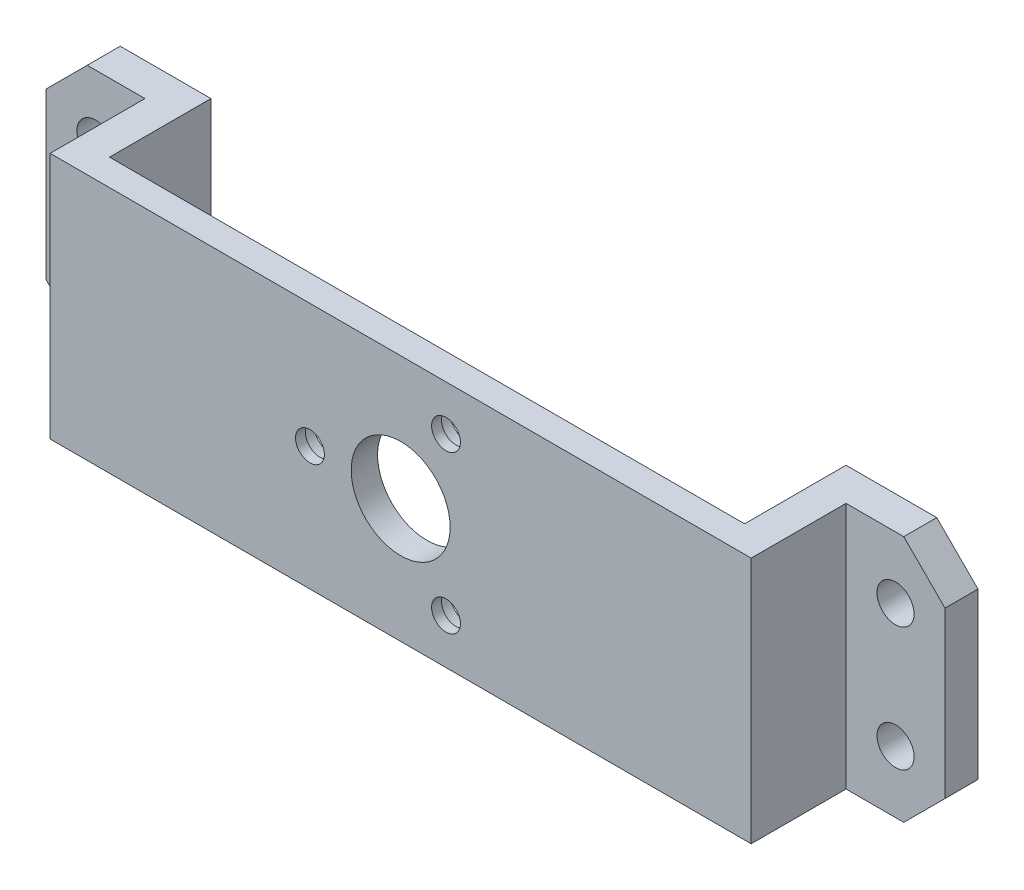
SolidWorks part; units mm, degrees
ref_plane "Front Plane" through (0, 0, 0) normal (0, 0, 1) x (1, 0, 0)
ref_plane "Top Plane" through (0, 0, 0) normal (0, 1, 0) x (1, 0, 0)
ref_plane "Right Plane" through (0, 0, 0) normal (1, 0, 0) x (0, 0, -1)
sketch "Sketch1" plane through (0, 0, 0) normal (0, 0, 1) x (1, 0, 0)
  line L1 (-42.5, -15) -> (42.5, -15)
  line L2 (-42.5, -15) -> (-42.5, 15)
  line L3 (-42.5, 15) -> (42.5, 15)
  line L4 (42.5, -15) -> (42.5, 15)
  line L5 (-42.5, -15) -> (42.5, 15) construction
  line L6 (-42.5, 15) -> (42.5, -15) construction
  circle A0 centre (0, 0) radius 6
  point P0 (0, 0)
  dimension "D1" = 12
  dimension "D2" = 85
  dimension "D3" = 30
extrude "Boss-Extrude1" add sketch "Sketch1" along normal blind 3.2
sketch "Sketch5" plane through (0, 0, 3.2) normal (0, 0, 1) x (1, 0, 0)
  line L0 (0, 0) -> (-11, 0) construction
  line L1 (0, 0) -> (5.5, -9.5263) construction
  line L2 (0, 0) -> (5.5, 9.5263) construction
  circle A0 centre (0, 0) radius 11 construction
  circle A1 centre (5.5, 9.5263) radius 1.75
  circle A2 centre (-11, 0) radius 1.75
  circle A3 centre (5.5, -9.5263) radius 1.75
  dimension "D3" = 22
  dimension "D4" = 3.5
  dimension "D1" = 120
  dimension "D2" = 120
extrude "Cut-Extrude1" cut sketch "Sketch5" against normal through all
sketch "Sketch7" plane through (0, 0, 0) normal (0, 0, -1) x (-1, 0, 0)
  circle A0 centre (-5.5, 9.5263) radius 1.75 construction
  circle A1 centre (11, 0) radius 1.75 construction
  circle A2 centre (-5.5, -9.5263) radius 1.75 construction
  circle A3 centre (-5.5, 9.5263) radius 1.75 construction
  circle A4 centre (11, 0) radius 1.75 construction
  circle A5 centre (-5.5, -9.5263) radius 1.75 construction
  circle A6 centre (-5.5, 9.5263) radius 3
  circle A7 centre (11, 0) radius 3
  circle A8 centre (-5.5, -9.5263) radius 3
  dimension "D1" = 6
extrude "Cut-Extrude2" cut sketch "Sketch7" against normal blind 2
sketch "Sketch2" plane through (0, 0, 0) normal (0, 0, -1) x (-1, 0, 0)
  line L0 (-42.5, 15) -> (42.5, 15) construction
  line L1 (42.5, -15) -> (38.5, -15)
  line L2 (42.5, -15) -> (42.5, 15)
  line L3 (42.5, 15) -> (38.5, 15)
  line L4 (38.5, -15) -> (38.5, 15)
  line L5 (0, 0) -> (-38.5, 0) construction
  line L6 (-42.5, -15) -> (-38.5, -15)
  line L7 (-42.5, -15) -> (-42.5, 15)
  line L8 (-42.5, 15) -> (-38.5, 15)
  line L9 (-38.5, -15) -> (-38.5, 15)
  line L10 (0, 0) -> (38.5, 0) construction
  dimension "D1" = 4
extrude "Boss-Extrude2" add sketch "Sketch2" along normal offset from surface (12.3 mm away) 15.5 up to face at (7.25, 9.5263, 3.2)
sketch "Sketch3" plane through (0, 0, -12.3) normal (0, 0, -1) x (-1, 0, 0)
  line L0 (42.5, 15) -> (38.5, 15) construction
  line L1 (38.5, -15) -> (54.5, -15)
  line L2 (38.5, -15) -> (38.5, 15)
  line L3 (38.5, 15) -> (54.5, 15)
  line L4 (54.5, -15) -> (54.5, 15)
  line L5 (-38.5, -15) -> (-54.5, -15)
  line L6 (-38.5, -15) -> (-38.5, 15)
  line L7 (-38.5, 15) -> (-54.5, 15)
  line L8 (-54.5, -15) -> (-54.5, 15)
  line L9 (-38.5, 15) -> (-42.5, 15) construction
  line L10 (42.5, -15) -> (42.5, 15) construction
  line L11 (42.5, -15) -> (42.5, 15) construction
  line L12 (42.5, 0) -> (54.5, 0) construction
  line L13 (48.5, 0) -> (48.5, 7.5) construction
  line L14 (-42.5, 15) -> (-42.5, -15) construction
  line L16 (-42.5, 15) -> (-42.5, -15) construction
  line L17 (-42.5, 0) -> (-54.5, 0) construction
  line L18 (-48.5, 0) -> (-48.5, 7.5) construction
  line L19 (-48.5, 7.5) -> (-48.5, 15) construction
  line L20 (-48.5, 0) -> (-48.5, -7.5) construction
  line L21 (-48.5, -7.5) -> (-48.5, -15) construction
  line L22 (48.5, 7.5) -> (48.5, 15) construction
  line L23 (48.5, 0) -> (48.5, -7.5) construction
  line L24 (48.5, -7.5) -> (48.5, -15) construction
  circle A6 centre (-48.5, 7.5) radius 2.25
  circle A7 centre (-48.5, 7.5) radius 4 construction
  circle A8 centre (-48.5, -7.5) radius 2.25
  circle A9 centre (-48.5, -7.5) radius 4 construction
  circle A10 centre (48.5, -7.5) radius 2.25
  circle A11 centre (48.5, 7.5) radius 2.25
  dimension "D1" = 12
  dimension "D2" = 15
  dimension "D3" = 97
  dimension "D5" = 4.5
  dimension "D6" = 8
extrude "Boss-Extrude3" add sketch "Sketch3" against normal blind 4
chamfer "Chamfer1" distance 5 angle 45 4 edges at (-54.5, 15, -10.3) (-54.5, -15, -10.3) (54.5, 15, -10.3) (54.5, -15, -10.3)
